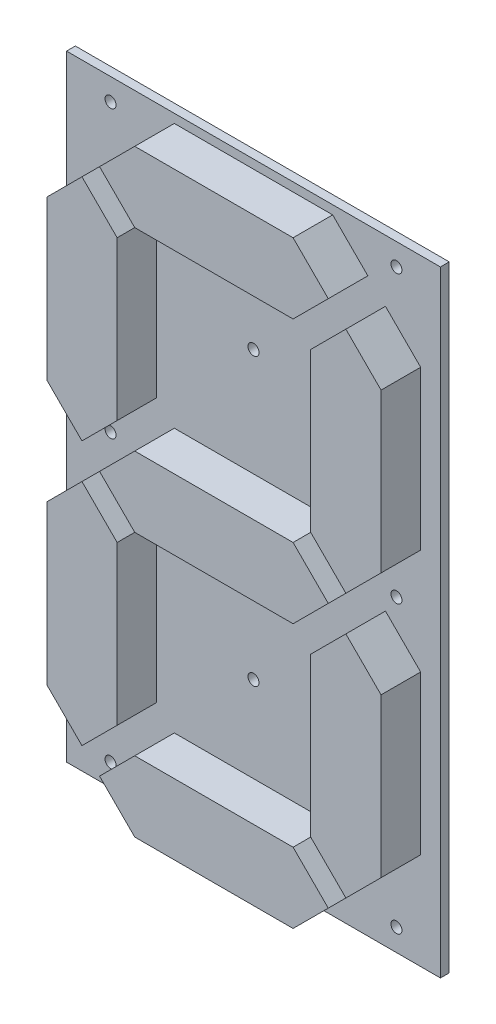
SolidWorks part; units mm, degrees
ref_plane "Alzado" through (0, 0, 0) normal (0, 0, 1) x (1, 0, 0)
ref_plane "Planta" through (0, 0, 0) normal (0, 1, 0) x (1, 0, 0)
ref_plane "Vista lateral" through (0, 0, 0) normal (1, 0, 0) x (0, 0, -1)
sketch "Croquis1" plane through (0, 0, 0) normal (0, 0, 1) x (1, 0, 0)
  line L0 (-42.5, 0) -> (42.5, 0) construction
  line L1 (-42.5, -70) -> (42.5, -70)
  line L2 (-42.5, -70) -> (-42.5, 70)
  line L3 (-42.5, 70) -> (42.5, 70)
  line L4 (42.5, -70) -> (42.5, 70)
  line L5 (-42.5, -70) -> (42.5, 70) construction
  line L6 (-42.5, 70) -> (42.5, -70) construction
  line L7 (-42.5, 70) -> (-42.5, 65) construction
  line L8 (-42.5, 65) -> (42.5, 65) construction
  line L9 (-42.5, 70) -> (-32.5, 70) construction
  line L10 (-32.5, 70) -> (-32.5, -70) construction
  line L11 (-42.5, -70) -> (-42.5, -65) construction
  line L12 (-42.5, -65) -> (42.5, -65) construction
  line L13 (42.5, -70) -> (32.5, -70) construction
  line L14 (32.5, -70) -> (32.5, 70) construction
  line L15 (-32.5, -65) -> (32.5, 0) construction
  line L16 (32.5, 0) -> (-32.5, 65) construction
  line L17 (-32.5, 65) -> (32.5, 65) construction
  line L18 (32.5, 65) -> (-32.5, 0) construction
  line L19 (-32.5, 0) -> (32.5, -65) construction
  circle A0 centre (-32.5, 65) radius 1.25
  circle A1 centre (32.5, 65) radius 1.25
  circle A2 centre (-32.5, 0) radius 1.25
  circle A3 centre (32.5, 0) radius 1.25
  circle A4 centre (-32.5, -65) radius 1.25
  circle A5 centre (32.5, -65) radius 1.25
  circle A6 centre (0, -32.5) radius 1.25
  circle A7 centre (0, 32.5) radius 1.25
  point P0 (0, 0)
extrude "Saliente-Extruir1" add sketch "Croquis1" along normal blind 2
sketch "Croquis2" plane through (0, 0, 2) normal (0, 0, 1) x (1, 0, 0)
  line L0 (-42.5, 0) -> (42.5, 0) construction
  line L1 (-42.5, 70) -> (-42.5, -70) construction
  line L2 (42.5, -70) -> (42.5, 70) construction
  line L3 (0, 70) -> (0, -70) construction
  line L4 (42.5, 70) -> (-42.5, 70) construction
  line L5 (-42.5, -70) -> (42.5, -70) construction
  line L6 (0, 0) -> (30, 0) construction
  line L7 (30, 0) -> (30, 4) construction
  line L8 (-30, 56) -> (-26, 56) construction
  line L9 (-26, 56) -> (-26, 60) construction
  line B0 (30, 4) -> (30, 12) construction
  line B1 (30, 12) -> (30, 48) construction
  line B2 (30, 48) -> (30, 56) construction
  line B3 (30, 12) -> (38, 12) construction
  line B4 (38, 12) -> (22, 12) construction
  line B5 (30, 48) -> (38, 48) construction
  line B6 (38, 48) -> (22, 48) construction
  line B7 (22, 48) -> (30, 56)
  line B8 (30, 56) -> (38, 48)
  line B9 (38, 48) -> (38, 12)
  line B10 (38, 12) -> (30, 4)
  line B11 (30, 4) -> (22, 12)
  line B12 (22, 12) -> (22, 48)
  line B13 (-22, 48) -> (-30, 56)
  line B14 (-30, 56) -> (-38, 48)
  line B15 (-38, 48) -> (-38, 12)
  line B16 (-38, 12) -> (-30, 4)
  line B17 (-30, 4) -> (-22, 12)
  line B18 (-22, 12) -> (-22, 48)
  line B19 (22, -48) -> (30, -56)
  line B20 (30, -56) -> (38, -48)
  line B21 (38, -48) -> (38, -12)
  line B22 (38, -12) -> (30, -4)
  line B23 (30, -4) -> (22, -12)
  line B24 (22, -12) -> (22, -48)
  line B25 (-22, -48) -> (-30, -56)
  line B26 (-30, -56) -> (-38, -48)
  line B27 (-38, -48) -> (-38, -12)
  line B28 (-38, -12) -> (-30, -4)
  line B29 (-30, -4) -> (-22, -12)
  line B30 (-22, -12) -> (-22, -48)
  line B31 (-18, -8) -> (-26, 0)
  line B32 (-26, 0) -> (-18, 8)
  line B33 (-18, 8) -> (18, 8)
  line B34 (18, 8) -> (26, 0)
  line B35 (26, 0) -> (18, -8)
  line B36 (18, -8) -> (-18, -8)
  line B37 (-18, 52) -> (-26, 60)
  line B38 (-26, 60) -> (-18, 68)
  line B39 (-18, 68) -> (18, 68)
  line B40 (18, 68) -> (26, 60)
  line B41 (26, 60) -> (18, 52)
  line B42 (18, 52) -> (-18, 52)
  line B43 (-18, -52) -> (-26, -60)
  line B44 (-26, -60) -> (-18, -68)
  line B45 (-18, -68) -> (18, -68)
  line B46 (18, -68) -> (26, -60)
  line B47 (26, -60) -> (18, -52)
  line B48 (18, -52) -> (-18, -52)
sketch_block_instance "Bloque1-1"
sketch_block "Bloque1"
sketch_block_instance "Bloque1-3"
sketch_block_instance "Bloque1-4"
sketch_block_instance "Bloque1-5"
sketch_block_instance "Bloque1-6"
sketch_block_instance "Bloque1-7"
sketch_block_instance "Bloque1-8"
extrude "Saliente-Extruir2" add sketch "Croquis2" along normal blind 9
